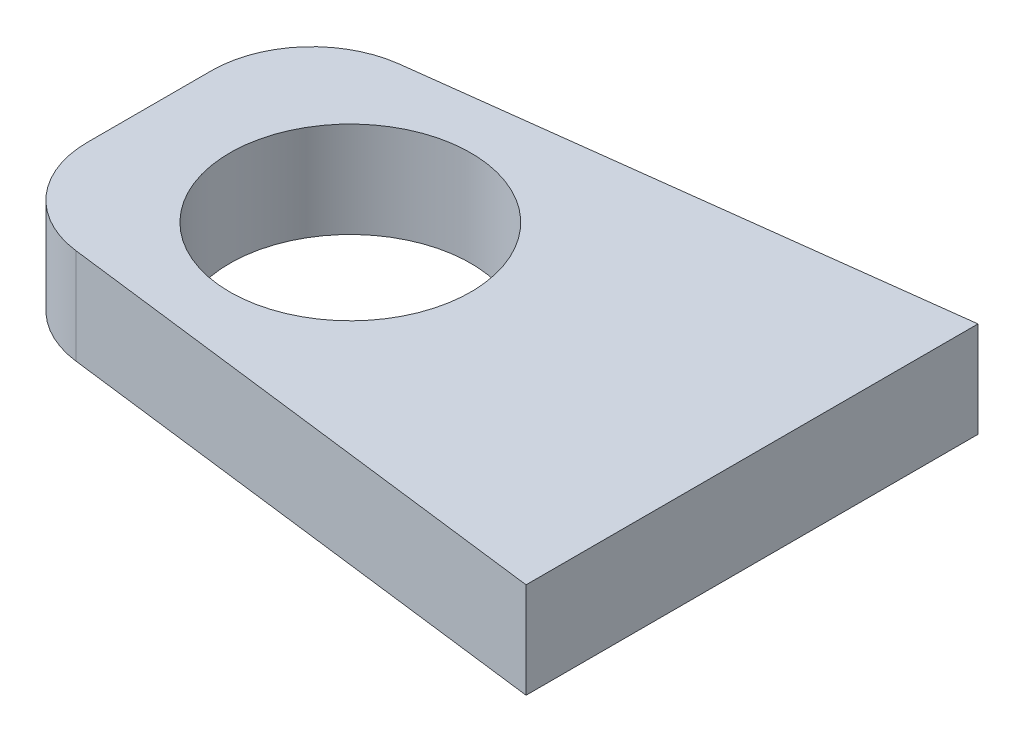
SolidWorks part; units mm, degrees
ref_plane "Front Plane" through (0, 0, 0) normal (0, 0, 1) x (1, 0, 0)
ref_plane "Top Plane" through (0, 0, 0) normal (0, 1, 0) x (1, 0, 0)
ref_plane "Right Plane" through (0, 0, 0) normal (1, 0, 0) x (0, 0, -1)
sketch "Sketch1" plane through (0, 0, 0) normal (0, 1, 0) x (1, 0, 0)
  line L0 (0, -11.25) -> (0, 11.25)
  line L1 (0, 11.25) -> (-30, 7.5)
  line L2 (-30, 7.5) -> (-30, -7.5)
  line L3 (-30, -7.5) -> (0, -11.25)
  line L4 (-30, 0) -> (0, 0) construction
  circle A0 centre (-20, 0) radius 6
  point P3 (0, 0)
  point P4 (0, 0)
  point P12 (0, 0)
  dimension "D5" = 12
  dimension "D1" = 22.5
  dimension "D2" = 15
  dimension "D3" = 30
  dimension "D6" = 10
extrude "Boss-Extrude1" add sketch "Sketch1" along normal blind 4.7625
fillet "Fillet1" radius 5 2 edges at (-30, 2.3813, 7.5) (-30, 2.3813, -7.5)
equation "\"steeringarmlength\"=50"
equation "\"mountingholespacing\"=15"
